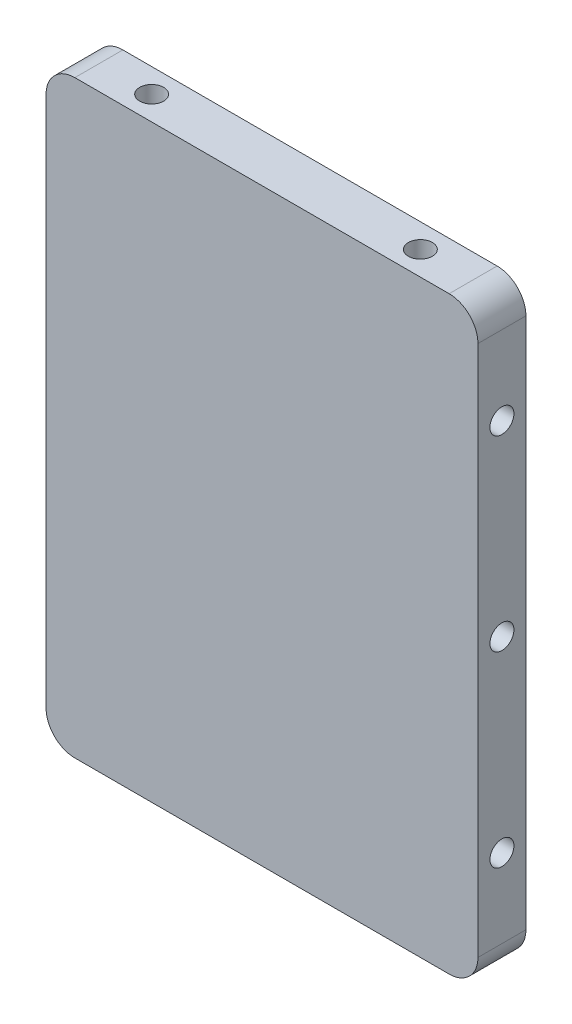
SolidWorks part; units mm, degrees
material "6063-T5"
ref_plane "前视基准面" through (0, 0, 0) normal (0, 0, 1) x (1, 0, 0)
ref_plane "上视基准面" through (0, 0, 0) normal (0, 1, 0) x (1, 0, 0)
ref_plane "右视基准面" through (0, 0, 0) normal (1, 0, 0) x (0, 0, -1)
other "Configuration Table"
sketch "草图1" plane through (0, 0, 0) normal (0, 0, 1) x (1, 0, 0)
  line L1 (-22.5, -30.7) -> (22.5, -30.7)
  line L2 (-22.5, -30.7) -> (-22.5, 30.7)
  line L3 (-22.5, 30.7) -> (22.5, 30.7)
  line L4 (22.5, -30.7) -> (22.5, 30.7)
  line L5 (-22.5, -30.7) -> (22.5, 30.7) construction
  line L6 (-22.5, 30.7) -> (22.5, -30.7) construction
  point P0 (0, 0)
  dimension "D1" = 45
  dimension "D2" = 61.4
extrude "凸台-拉伸1" add sketch "草图1" along normal blind 5
hole_wizard "M3 螺纹孔1" positions "草图2" profile "草图3" tap size "M3" standard "GB"
sketch "草图2" plane through (-22.5, 0, 0) normal (-1, 0, 0) x (0, 0, 1)
  line L0 (2.5, 30.7) -> (2.5, -30.7) construction
  line L1 (5, 30.7) -> (0, 30.7) construction
  line L2 (5, -30.7) -> (0, -30.7) construction
  point P0 (2.5, 0)
cosmetic thread "孔螺蚊线1" parameters "D1"=6, "D2"=3
sketch "草图3" plane through (-22.5, 0, 2.5) normal (0, 1, 0) x (0, 0, 1)
  line L0 (0, 0) -> (0, 5.7511)
  line L1 (0, 5.7511) -> (1.25, 5)
  line L2 (1.25, 5) -> (1.25, 0)
  line L5 (1.25, 0) -> (0, 0)
  line L10 (0, 5.7511) -> (-1.25, 5) construction
  line L11 (0, -6.35) -> (0, 107.95) construction
  dimension "螺纹孔钻头直径" = 2.5
  dimension "螺纹孔钻头深度" = 5
  dimension "导头角度" = 118
hole_wizard "M3 螺纹孔2" positions "草图4" profile "草图5" tap size "M3" standard "GB"
sketch "草图4" plane through (-22.5, 0, 0) normal (-1, 0, 0) x (0, 0, 1)
  line L0 (2.5, 19.5) -> (2.5, 0) construction
  point P0 (2.5, 19.5)
  dimension "D1" = 19.5
cosmetic thread "孔螺蚊线2" parameters "D1"=6, "D2"=3
sketch "草图5" plane through (-22.5, 19.5, 2.5) normal (0, 1, 0) x (0, 0, 1)
  line L0 (0, 0) -> (0, 5.7511)
  line L1 (0, 5.7511) -> (1.25, 5)
  line L2 (1.25, 5) -> (1.25, 0)
  line L5 (1.25, 0) -> (0, 0)
  line L10 (0, 5.7511) -> (-1.25, 5) construction
  line L11 (0, -6.35) -> (0, 107.95) construction
  dimension "螺纹孔钻头直径" = 2.5
  dimension "螺纹孔钻头深度" = 5
  dimension "导头角度" = 118
mirror "镜向1" about plane through (0, 0, 0) normal (0, 1, 0) of "M3 螺纹孔2"
hole_wizard "M3 螺纹孔3" positions "草图7" profile "草图8" tap size "M3" standard "GB" end condition through all
sketch "草图7" plane through (0, -30.7, 0) normal (0, -1, 0) x (-1, 0, 0)
  line L0 (-15.3347, -2.5) -> (49984.6653, -2.5) construction
  line L1 (22.5, -5) -> (22.5, 0) construction
  point P0 (-14, -2.5)
  point P6 (22.5, -2.5)
  dimension "D1" = 14
sketch "草图8" plane through (14, -30.7, 2.5) normal (1, 0, 0) x (0, 0, -1)
  line L0 (0, 0) -> (0, 61.4)
  line L1 (0, 61.4) -> (1.25, 61.4)
  line L2 (1.25, 61.4) -> (1.25, 0)
  line L5 (1.25, 0) -> (0, 0)
  line L11 (0, -6.35) -> (0, 107.95) construction
  dimension "通孔螺纹孔钻头直径" = 2.5
  dimension "通孔螺纹孔钻头深度" = 61.4
cosmetic thread "孔螺蚊线3" parameters "D2"=3
mirror "镜向2" about plane through (0, 0, 0) normal (1, 0, 0) of "M3 螺纹孔3"
mirror "镜向3" about plane through (0, 0, 0) normal (1, 0, 0) of "镜向1", "M3 螺纹孔2", "M3 螺纹孔1"
hole_wizard "M3 螺纹孔4" positions "草图10" profile "草图11" tap size "M3" standard "GB" end condition through all
sketch "草图10" plane through (0, 30.7, 0) normal (0, 1, 0) x (1, 0, 0)
  point P0 (-14, -2.5)
  point P3 (14, -2.5)
sketch "草图11" plane through (-14, 30.7, 2.5) normal (1, 0, 0) x (0, 0, 1)
  line L0 (0, 0) -> (0, 61.4)
  line L1 (0, 61.4) -> (1.25, 61.4)
  line L2 (1.25, 61.4) -> (1.25, 0)
  line L5 (1.25, 0) -> (0, 0)
  line L11 (0, -6.35) -> (0, 107.95) construction
  dimension "通孔螺纹孔钻头直径" = 2.5
  dimension "通孔螺纹孔钻头深度" = 61.4
fillet "圆角1" radius 3 4 edges at (22.5, -30.7, 2.5) (-22.5, -30.7, 2.5) (22.5, 30.7, 2.5) (-22.5, 30.7, 2.5)
